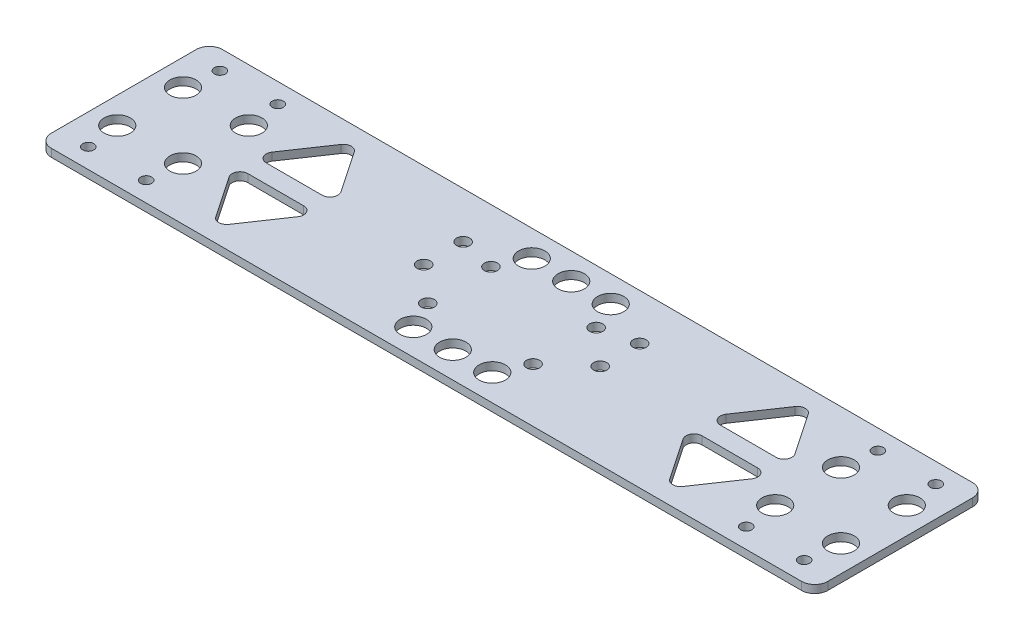
SolidWorks part; units mm, degrees
material "A-玻璃纤维"
ref_plane "前视基准面" through (0, 0, 0) normal (0, 0, 1) x (1, 0, 0)
ref_plane "上视基准面" through (0, 0, 0) normal (0, 1, 0) x (1, 0, 0)
ref_plane "右视基准面" through (0, 0, 0) normal (1, 0, 0) x (0, 0, -1)
sketch "草图1" plane through (0, 0, 0) normal (0, 1, 0) x (1, 0, 0)
  line L0 (0, 32.5) -> (0, -32.5) construction
  line L1 (-147.5, 32.5) -> (147.5, 32.5)
  line L2 (-147.5, 32.5) -> (-147.5, -32.5)
  line L3 (-147.5, -32.5) -> (147.5, -32.5)
  line L4 (147.5, 32.5) -> (147.5, -32.5)
  line L5 (-147.5, 32.5) -> (147.5, -32.5) construction
  line L6 (-147.5, -32.5) -> (147.5, 32.5) construction
  line L7 (-147.5, 0) -> (147.5, 0) construction
  line L8 (112.5, 12.5) -> (137.5, -12.5) construction
  line L9 (-137.5, 12.5) -> (-112.5, 12.5) construction
  line L10 (-137.5, 12.5) -> (-137.5, -12.5) construction
  line L11 (-137.5, -12.5) -> (-112.5, -12.5) construction
  line L12 (-112.5, 12.5) -> (-112.5, -12.5) construction
  line L13 (-137.5, 12.5) -> (-112.5, -12.5) construction
  line L14 (-137.5, -12.5) -> (-112.5, 12.5) construction
  line L15 (-20, 12) -> (20, 12) construction
  line L16 (-20, 12) -> (-20, -12) construction
  line L17 (-20, -12) -> (20, -12) construction
  line L18 (20, 12) -> (20, -12) construction
  line L19 (-20, 12) -> (20, -12) construction
  line L20 (-20, -12) -> (20, 12) construction
  line L21 (137.5, 12.5) -> (112.5, -12.5) construction
  circle A0 centre (-137.5, 12.5) radius 2.5
  circle A1 centre (-112.5, 12.5) radius 2.5
  circle A2 centre (-137.5, -12.5) radius 2.5
  circle A3 centre (-112.5, -12.5) radius 2.5
  circle A4 centre (-20, 12) radius 2.5
  circle A5 centre (-20, -12) radius 2.5
  circle A6 centre (20, -12) radius 2.5
  circle A7 centre (20, 12) radius 2.5
  circle A8 centre (112.5, -12.5) radius 2.5
  circle A9 centre (137.5, -12.5) radius 2.5
  circle A10 centre (112.5, 12.5) radius 2.5
  circle A11 centre (137.5, 12.5) radius 2.5
  point P0 (0, 0)
  point P10 (-125, 0)
  point P19 (0, 0)
  point P36 (125, 0)
  dimension "D3" = 250
  dimension "D6" = 5
  dimension "D7" = 5
  dimension "D1" = 25
  dimension "D2" = 25
  dimension "D4" = 40
  dimension "D5" = 24
  dimension "D8" = 10
  dimension "D9" = 20
extrude "凸台-拉伸1" add sketch "草图1" along normal blind 3
sketch "草图2" plane through (0, 0, 0) normal (0, -1, 0) x (1, 0, 0)
  line L0 (147.5, -32.5) -> (-147.5, -32.5) construction
  line L1 (-147.5, 32.5) -> (-100, 32.5)
  line L2 (-147.5, 32.5) -> (-147.5, -32.5)
  line L3 (-147.5, -32.5) -> (-100, -32.5)
  line L4 (-100, 32.5) -> (-100, -32.5)
  line L5 (0, 32.5) -> (0, -32.5) construction
  line L6 (-147.5, 32.5) -> (147.5, 32.5) construction
  line L7 (147.5, -32.5) -> (100, -32.5)
  line L8 (100, 32.5) -> (100, -32.5)
  line L9 (147.5, 32.5) -> (100, 32.5)
  line L10 (147.5, 32.5) -> (147.5, -32.5)
  circle A0 centre (-112.5, -12.5) radius 2.5 construction
  circle A1 centre (-137.5, -12.5) radius 2.5 construction
  circle A2 centre (-112.5, 12.5) radius 2.5 construction
  circle A3 centre (-137.5, 12.5) radius 2.5 construction
  circle A4 centre (-112.5, -12.5) radius 2.5
  circle A5 centre (-137.5, -12.5) radius 2.5
  circle A6 centre (-112.5, 12.5) radius 2.5
  circle A7 centre (-137.5, 12.5) radius 2.5
  circle A8 centre (137.5, -12.5) radius 2.5 construction
  circle A9 centre (112.5, -12.5) radius 2.5 construction
  circle A10 centre (137.5, 12.5) radius 2.5 construction
  circle A11 centre (112.5, 12.5) radius 2.5 construction
  circle A12 centre (137.5, -12.5) radius 2.5
  circle A13 centre (112.5, -12.5) radius 2.5
  circle A14 centre (137.5, 12.5) radius 2.5
  circle A15 centre (112.5, 12.5) radius 2.5
  dimension "D1" = 200
extrude "凸台-拉伸2" [suppressed] add sketch "草图2" along normal blind 29
sketch "草图4" plane through (0, 3, 0) normal (0, 1, 0) x (1, 0, 0)
  line L0 (0, -32.5) -> (0, 32.5) construction
  line L1 (-147.5, -32.5) -> (147.5, -32.5) construction
  line L2 (147.5, 32.5) -> (-147.5, 32.5) construction
  circle A0 centre (112.5, -12.5) radius 5
  circle A1 centre (112.5, 12.5) radius 5
  circle A2 centre (137.5, -12.5) radius 5
  circle A3 centre (137.5, 12.5) radius 5
  circle A4 centre (-137.5, 12.5) radius 5
  circle A5 centre (-137.5, -12.5) radius 5
  circle A6 centre (-112.5, 12.5) radius 5
  circle A7 centre (-112.5, -12.5) radius 5
  dimension "D1" = 10
extrude "切除-拉伸2" cut sketch "草图4" against normal blind 15
sketch "草图5" plane through (0, 3, 0) normal (0, 1, 0) x (1, 0, 0)
  line L0 (0, 32.5) -> (0, -32.5) construction
  line L1 (147.5, 32.5) -> (-147.5, 32.5) construction
  line L2 (-147.5, -32.5) -> (147.5, -32.5) construction
  line L3 (-147.5, 0) -> (0, 0) construction
  line L4 (-147.5, 32.5) -> (-147.5, -32.5) construction
  line L5 (-137.5, 12.5) -> (-112.5, 12.5) construction
  line L6 (-105, -10) -> (-145, -10) construction
  line L7 (-105, -10) -> (-105, 10) construction
  line L8 (-105, 10) -> (-145, 10) construction
  line L9 (-145, -10) -> (-145, 10) construction
  line L10 (-105, -10) -> (-145, 10) construction
  line L11 (-105, 10) -> (-145, -10) construction
  circle A0 centre (-145, 10) radius 1.6
  circle A1 centre (-105, 10) radius 1.6
  circle A2 centre (-145, -10) radius 1.6
  circle A3 centre (-105, -10) radius 1.6
  circle A4 centre (105, 10) radius 1.6
  circle A5 centre (105, -10) radius 1.6
  circle A6 centre (145, -10) radius 1.6
  circle A7 centre (145, 10) radius 1.6
  point P11 (-125, 0)
  point P20 (-125, 12.5)
  dimension "D3" = 3.2
  dimension "D1" = 40
  dimension "D2" = 20
extrude "切除-拉伸3" [suppressed] cut sketch "草图5" against normal blind 7
sketch "草图6" plane through (0, 3, 0) normal (0, 1, 0) x (1, 0, 0)
  line L0 (0, -48.7404) -> (0, 56.7128) construction
  line L1 (194.5991, 0) -> (-225.7639, 0) construction
  circle A0 centre (136, -25) radius 2.1
  circle A1 centre (-136, -25) radius 2.1
  circle A2 centre (-136, 25) radius 2.1
  circle A3 centre (136, 25) radius 2.1
  circle A4 centre (114, -25) radius 2.1
  circle A5 centre (-114, -25) radius 2.1
  circle A6 centre (114, 25) radius 2.1
  circle A7 centre (-114, 25) radius 2.1
  dimension "D1" = 4.2
  dimension "D2" = 50
  dimension "D3" = 22
  dimension "D4" = 272
extrude "切除-拉伸4" cut sketch "草图6" against normal blind 10
sketch "草图7" plane through (0, 3, 0) normal (0, 1, 0) x (1, 0, 0)
  line L0 (0, 41.8503) -> (0, -42.7639) construction
  line L1 (-161.943, 0) -> (160.5684, 0) construction
  line L2 (-86.25, 27.5) -> (-102.5, 3.5)
  line L3 (-102.5, 3.5) -> (-70, 3.5)
  line L4 (-70, 3.5) -> (-86.25, 27.5)
  line L5 (-66.25, 19.5) -> (-66.25, 48.8436) construction
  line L6 (-30, 3.5) -> (-62.5, 3.5)
  line L7 (-46.25, 27.5) -> (-30, 3.5)
  line L8 (-62.5, 3.5) -> (-46.25, 27.5)
  line L9 (-86.25, 27.5) -> (-86.25, -18.7836) construction
  line L10 (-102.5, -3.5) -> (-70, -3.5)
  line L11 (-86.25, -27.5) -> (-102.5, -3.5)
  line L12 (-70, -3.5) -> (-86.25, -27.5)
  line L13 (-46.25, -27.5) -> (-30, -3.5)
  line L14 (-62.5, -3.5) -> (-46.25, -27.5)
  line L15 (-30, -3.5) -> (-62.5, -3.5)
  line L16 (46.25, 27.5) -> (30, 3.5)
  line L17 (62.5, 3.5) -> (46.25, 27.5)
  line L18 (30, 3.5) -> (62.5, 3.5)
  line L19 (102.5, 3.5) -> (70, 3.5)
  line L20 (86.25, 27.5) -> (102.5, 3.5)
  line L21 (70, 3.5) -> (86.25, 27.5)
  line L22 (86.25, -27.5) -> (102.5, -3.5)
  line L23 (70, -3.5) -> (86.25, -27.5)
  line L24 (102.5, -3.5) -> (70, -3.5)
  line L25 (62.5, -3.5) -> (46.25, -27.5)
  line L26 (30, -3.5) -> (62.5, -3.5)
  line L27 (46.25, -27.5) -> (30, -3.5)
  line L28 (147.5, 32.5) -> (-147.5, 32.5) construction
  line L29 (-30, 22.5) -> (-15, 22.5) construction
  line L30 (-15, 22.5) -> (0, 22.5) construction
  circle A0 centre (-66.25, 19.5) radius 7.5
  circle A1 centre (-66.25, -19.5) radius 7.5
  circle A2 centre (66.25, 19.5) radius 7.5
  circle A3 centre (66.25, -19.5) radius 7.5
  circle A4 centre (-112.5, 12.5) radius 5 construction
  circle A5 centre (-20, -12) radius 2.5 construction
  circle A6 centre (-30, 22.5) radius 5
  circle A7 centre (-15, 22.5) radius 5
  circle A8 centre (15, 22.5) radius 5
  circle A9 centre (30, 22.5) radius 5
  circle A10 centre (-30, -22.5) radius 5
  circle A11 centre (-15, -22.5) radius 5
  circle A12 centre (15, -22.5) radius 5
  circle A13 centre (30, -22.5) radius 5
  circle A14 centre (0, 22.5) radius 5
  circle A15 centre (0, -22.5) radius 5
  dimension "D5" = 20
  dimension "D6" = 15
  dimension "D7" = 13
  dimension "D8" = 10
  dimension "D9" = 10
  dimension "D10" = 60
  dimension "D1" = 10
  dimension "D2" = 7
  dimension "D3" = 5
  dimension "D4" = 10
extrude "切除-拉伸5" cut sketch "草图7" against normal blind 10
fillet "圆角1" radius 3 24 edges at (-102.5, 1.5, -3.5) (-86.25, 1.5, -27.5) (-70, 1.5, -3.5) (-30, 1.5, 3.5) (-46.25, 1.5, 27.5) (-62.5, 1.5, 3.5) (30, 1.5, -3.5) (46.25, 1.5, -27.5) (62.5, 1.5, -3.5) (-70, 1.5, 3.5) (-86.25, 1.5, 27.5) (-62.5, 1.5, -3.5) (-46.25, 1.5, -27.5) (-30, 1.5, -3.5) (46.25, 1.5, 27.5) (30, 1.5, 3.5) (62.5, 1.5, 3.5) (102.5, 1.5, 3.5) (86.25, 1.5, 27.5) (70, 1.5, 3.5) (70, 1.5, -3.5) (86.25, 1.5, -27.5) (102.5, 1.5, -3.5) (-102.5, 1.5, 3.5)
fillet "圆角2" radius 5 4 edges at (147.5, 1.5, 32.5) (-147.5, 1.5, -32.5) (147.5, 1.5, -32.5) (-147.5, 1.5, 32.5)
sketch "草图8" plane through (0, 0, 0) normal (0, -1, 0) x (1, 0, 0)
  line L0 (-88.7341, 23.8311) -> (-99.3299, 8.182)
  line L1 (-96.8458, 3.5) -> (-75.6542, 3.5)
  line L2 (-73.1701, 8.182) -> (-83.7659, 23.8311)
  arc A0 (-99.3299, 8.182) -> (-96.8458, 3.5) centre (-96.8458, 6.5) ccw
  arc A1 (-75.6542, 3.5) -> (-73.1701, 8.182) centre (-75.6542, 6.5) ccw
  arc A2 (-83.7659, 23.8311) -> (-88.7341, 23.8311) centre (-86.25, 22.1491) ccw
  dimension "D1" = 3
  dimension "D2" = 3
  dimension "D3" = 3
extrude "凸台-拉伸3" add sketch "草图8" against normal up to surface (3 mm away) up to face at (86.25, 3, -11.8083)
sketch "草图9" plane through (0, 0, 0) normal (0, -1, 0) x (1, 0, 0)
  line L0 (-88.7341, -23.8311) -> (-99.3299, -8.182)
  line L1 (-96.8458, -3.5) -> (-75.6542, -3.5)
  line L2 (-73.1701, -8.182) -> (-83.7659, -23.8311)
  arc A0 (-99.3299, -8.182) -> (-96.8458, -3.5) centre (-96.8458, -6.5) cw
  arc A1 (-75.6542, -3.5) -> (-73.1701, -8.182) centre (-75.6542, -6.5) cw
  arc A2 (-83.7659, -23.8311) -> (-88.7341, -23.8311) centre (-86.25, -22.1491) cw
  dimension "D1" = 3
  dimension "D2" = 3
  dimension "D3" = 3
extrude "凸台-拉伸4" add sketch "草图9" against normal up to surface (3 mm away) up to face at (86.25, 3, -11.8083)
sketch "草图10" plane through (0, 0, 0) normal (0, -1, 0) x (1, 0, 0)
  circle A0 centre (-66.25, -19.5) radius 7.5
  circle A1 centre (-66.25, 19.5) radius 7.5
extrude "凸台-拉伸5" add sketch "草图10" against normal up to surface (3 mm away) up to face at (86.25, 3, -11.8083)
sketch "草图12" plane through (0, 0, 0) normal (0, -1, 0) x (1, 0, 0)
  circle A0 centre (-20, -12) radius 2.4983
  circle A1 centre (-20, 12) radius 2.5
  circle A2 centre (20, -12) radius 2.5
  circle A3 centre (20, 12) radius 2.5
extrude "凸台-拉伸6" add sketch "草图12" against normal up to surface (3 mm away) up to face at (86.25, 3, -11.8083)
sketch "草图14" plane through (0, 0, 0) normal (0, -1, 0) x (1, 0, 0)
  circle A0 centre (66.25, -19.5) radius 7.5
  circle A1 centre (66.25, 19.5) radius 7.5
extrude "凸台-拉伸7" add sketch "草图14" against normal up to surface (3 mm away) up to face at (86.25, 3, -11.8083)
sketch "草图16" plane through (0, 3, 0) normal (0, 1, 0) x (1, 0, 0)
  circle A0 centre (-20, -12) radius 2.5
  circle A1 centre (-20, 12) radius 2.5
  circle A2 centre (20, -12) radius 2.5
  circle A3 centre (20, 12) radius 2.5
extrude "切除-拉伸9" cut sketch "草图16" against normal through all
mirror "镜向4" about plane through (0, 0, 0) normal (1, 0, 0) of "圆角1", "切除-拉伸5"
sketch "草图17" plane through (0, 3, 0) normal (0, 1, 0) x (1, 0, 0)
  line L0 (-48.7341, 23.8311) -> (-59.3299, 8.182)
  line L1 (-35.6542, 3.5) -> (-56.8458, 3.5)
  line L2 (-43.7659, 23.8311) -> (-33.1701, 8.182)
  line L3 (-33.1701, 8.182) -> (-43.7659, 23.8311) construction
  line L4 (-56.8458, -3.5) -> (-35.6542, -3.5)
  line L5 (-33.1701, -8.182) -> (-43.7659, -23.8311)
  line L7 (-48.7341, -23.8311) -> (-59.3299, -8.182)
  line L8 (43.7659, 23.8311) -> (33.1701, 8.182)
  line L9 (35.6542, 3.5) -> (56.8458, 3.5)
  line L10 (59.3299, 8.182) -> (48.7341, 23.8311)
  line L11 (35.6542, -3.5) -> (56.8458, -3.5)
  line L12 (59.3299, -8.182) -> (48.7341, -23.8311)
  line L13 (43.7659, -23.8311) -> (33.1701, -8.182)
  circle A0 centre (-66.25, 19.5) radius 7.5
  circle A1 centre (-66.25, -19.5) radius 7.5
  circle A2 centre (66.25, 19.5) radius 7.5
  circle A3 centre (66.25, -19.5) radius 7.5
  arc A4 (-59.3299, 8.182) -> (-56.8458, 3.5) centre (-56.8458, 6.5) ccw
  arc A5 (-35.6542, 3.5) -> (-33.1701, 8.182) centre (-35.6542, 6.5) ccw
  arc A6 (-43.7659, 23.8311) -> (-48.7341, 23.8311) centre (-46.25, 22.1491) ccw construction
  arc A7 (-43.7659, 23.8311) -> (-48.7341, 23.8311) centre (-46.25, 22.1491) ccw
  arc A9 (-56.8458, -3.5) -> (-59.3299, -8.182) centre (-56.8458, -6.5) ccw
  arc A10 (-48.7341, -23.8311) -> (-43.7659, -23.8311) centre (-46.25, -22.1491) ccw
  arc A11 (-35.6542, -3.5) -> (-33.1701, -8.182) centre (-35.6542, -6.5) cw
  arc A12 (43.7659, 23.8311) -> (48.7341, 23.8311) centre (46.25, 22.1491) cw
  arc A13 (59.3299, 8.182) -> (56.8458, 3.5) centre (56.8458, 6.5) cw
  arc A14 (35.6542, 3.5) -> (33.1701, 8.182) centre (35.6542, 6.5) cw
  arc A15 (35.6542, -3.5) -> (33.1701, -8.182) centre (35.6542, -6.5) ccw
  arc A16 (43.7659, -23.8311) -> (48.7341, -23.8311) centre (46.25, -22.1491) ccw
  arc A17 (59.3299, -8.182) -> (56.8458, -3.5) centre (56.8458, -6.5) ccw
  dimension "D1" = 3
  dimension "D2" = 3
  dimension "D3" = 3
  dimension "D4" = 3
  dimension "D5" = 3
  dimension "D6" = 3
  dimension "D7" = 3
  dimension "D8" = 3
  dimension "D9" = 3
  dimension "D10" = 3
  dimension "D11" = 3
  dimension "D12" = 3
extrude "凸台-拉伸9" add sketch "草图17" against normal up to surface (3 mm away) up to face at (-86.25, 0, 11.8083)
sketch "草图18" plane through (0, 0, 0) normal (0, -1, 0) x (1, 0, 0)
  circle A0 centre (-30, -22.5) radius 5
  circle A1 centre (30, -22.5) radius 5
  circle A2 centre (30, 22.5) radius 5
  circle A3 centre (-30, 22.5) radius 5
extrude "凸台-拉伸10" add sketch "草图18" against normal blind 3
sketch "草图19" plane through (0, 0, 0) normal (0, -1, 0) x (-1, 0, 0)
  circle A0 centre (-33.5, 15) radius 2.5
  circle A1 centre (-33.5, 0) radius 2.5
  circle A2 centre (33.5, 14.937) radius 2.5
  circle A3 centre (33.5, -0.063) radius 2.5
extrude "切除-拉伸10" cut sketch "草图19" against normal blind 10
